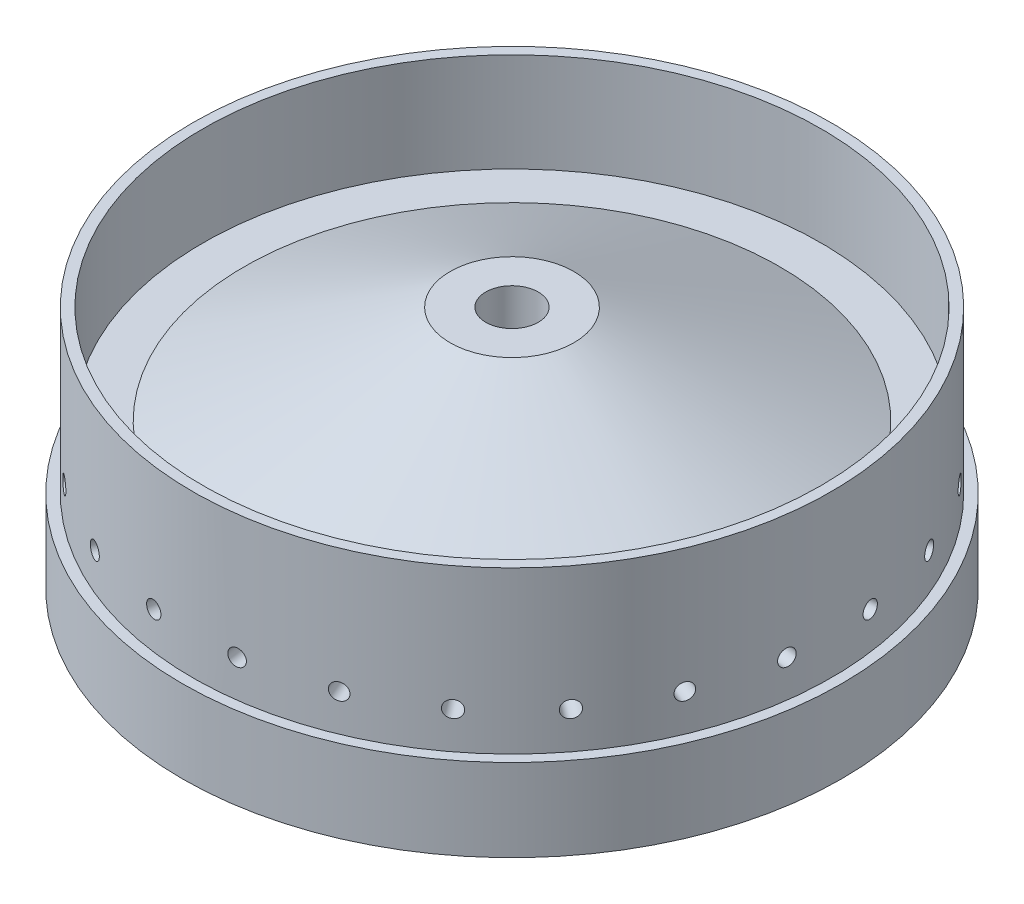
SolidWorks part; units mm, degrees
material "6061-T6 (SS)"
ref_plane "Front Plane" through (0, 0, 0) normal (0, 0, 1) x (1, 0, 0)
ref_plane "Top Plane" through (0, 0, 0) normal (0, 1, 0) x (1, 0, 0)
ref_plane "Right Plane" through (0, 0, 0) normal (1, 0, 0) x (0, 0, -1)
ref_plane "Plane1" through (0, 0, -75.0887) normal (0, 0, 1) x (1, 0, 0)
sketch "Sketch1" plane through (0, 0, 0) normal (0, 1, 0) x (1, 0, 0)
  line L1 (95.25, 0) -> (101.6, 0)
  line L2 (0, 0) -> (0, 61.9125) construction
  line L4 (101.6, 59.4931) -> (101.6, 0)
  line L6 (101.6, 59.4931) -> (8.0962, 59.4931) construction
  line L8 (0, 75.0887) -> (101.6, 75.0887)
  line L9 (101.6, 75.0887) -> (101.6, 59.4931)
  line L10 (8.0962, 0) -> (8.0962, 75.0887)
  line L11 (8.0962, 75.0887) -> (-8.0962, 75.0887)
  line L12 (-8.0962, 75.0887) -> (-8.0962, 0)
  line L13 (-8.0962, 0) -> (8.0962, 0)
  line L14 (8.0962, 59.4931) -> (0, 59.4931) construction
  line L15 (19.05, 75.0887) -> (82.55, 44.6088)
  line L16 (82.55, 44.6088) -> (95.25, 44.6088)
  line L17 (95.25, 44.6088) -> (95.25, 75.0887)
  ellipse E0 centre (0, 0) end of major axis (-95.25, 0) minor radius 59.4931
  point P18 (19.05, 75.0887)
  dimension "D4" = 15.5956
  dimension "D6" = 16.1925
  dimension "D7" = 6.35
  dimension "D8" = 30.48
  dimension "D9" = 12.7
  dimension "D10" = 19.05
  dimension "D2" = 101.6
  dimension "D3" = 75.0887
revolve "Revolve1" add sketch "Sketch1" angle 360 about L2
sketch "Sketch3" plane through (0, 0, 0) normal (0, 0, -1) x (-1, 0, 0)
  circle A0 centre (0, 0) radius 101.6
  circle A1 centre (0, 0) radius 98.425
  dimension "D1" = 203.2
  dimension "D2" = 3.175
extrude "Cut-Extrude2" cut sketch "Sketch3" along normal through all from offset 25.4
hole_wizard "1/4-20 Tapped Hole1" positions "3DSketch1" profile "Sketch10" tap size "1/4-20" standard "ANSI Inch"
sketch3d "3DSketch1"
  line L0 (97.583, 12.847, -36.83) -> (97.583, 12.847, 0) construction
  line L1 (97.583, 12.847, 0) -> (0, 0, 0) construction
  line L2 (0, 0, 0) -> (101.6, 0, 0) construction
  circle A0 centre (0, 0, 0) radius 101.6 construction
  point P0 (97.583, 12.847, -36.83)
  point P12 (0, 0, 101.6)
  dimension "D1" = 36.83
  dimension "D2" = 7.5
sketch "Sketch10" plane through (97.583, 12.847, -36.83) normal (0, 0, 1) x (-0.1305, 0.9914, 0)
  line L0 (0, 0) -> (0, 14.2338)
  line L1 (0, 14.2338) -> (2.5527, 12.7)
  line L2 (2.5527, 12.7) -> (2.5527, 0)
  line L5 (2.5527, 0) -> (0, 0)
  line L10 (0, 14.2338) -> (-2.5527, 12.7) construction
  line L11 (0, -6.35) -> (0, 107.95) construction
  dimension "Tap Drill Dia." = 5.1054
  dimension "Tap Drill Depth" = 12.7
  dimension "Drill Angle" = 118
cosmetic thread "Hole Thread2" parameters "D1"=12.7, "D2"=6.35
pattern_circular "CirPattern1" count 24 over 360 of "1/4-20 Tapped Hole1"
sketch "Sketch13" plane through (0, 0, 0) normal (0, 0, 1) x (1, 0, 0)
  line L0 (-67.9108, -66.7883) -> (66.7883, 67.9108)
  line L1 (-66.7883, -67.9108) -> (67.9108, 66.7883)
  line L2 (0, 0) -> (0, -28.3739) construction
  circle A4 centre (0, 0) radius 95.25 construction
  arc A5 (-67.9108, -66.7883) -> (-66.7883, -67.9108) centre (0, 0) ccw
  arc A6 (66.7883, 67.9108) -> (67.9108, 66.7883) centre (0, 0) cw
  dimension "D1" = 1.5875
  dimension "D2" = 135
sketch "Sketch14" plane through (0, 0, -75.0888) normal (0, 0, -1) x (-1, 0, 0)
  circle A0 centre (0, 0) radius 8.0962
  circle A1 centre (0, 0) radius 8.0962 construction
move or copy body "Body-Move/Copy1" bodies to move or copy 120 copy no rotation origin (0, 0, -37.5444) rotation axis (1, 0, 0) rotation angle 90
equation "\"D7@Sketch1\"= .25"
equation "\"D1@Plane1\"= \"D3@Sketch1\""
